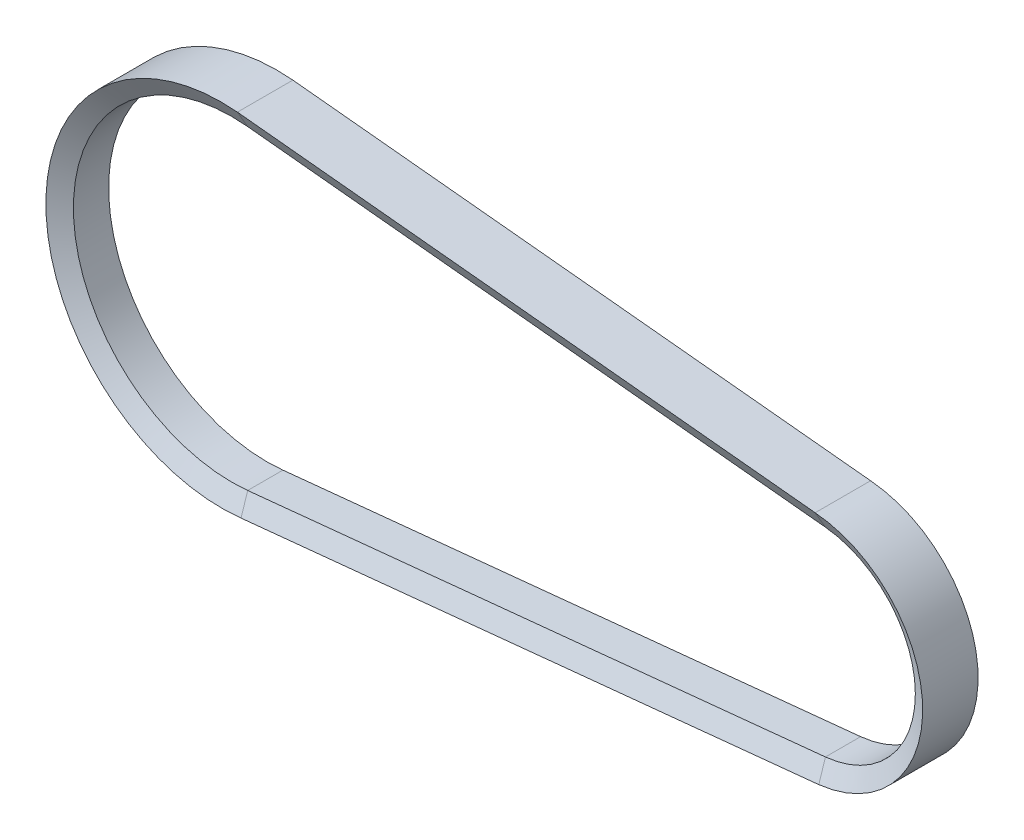
SolidWorks part; units mm, degrees
ref_plane "Front Plane" through (0, 0, 0) normal (0, 0, 1) x (1, 0, 0)
ref_plane "Top Plane" through (0, 0, 0) normal (0, 1, 0) x (1, 0, 0)
ref_plane "Right Plane" through (0, 0, 0) normal (1, 0, 0) x (0, 0, -1)
sketch "Sketch2" plane through (0, 0, 0) normal (0, 0, 1) x (1, 0, 0)
  line L0 (0, 0) -> (1, 0) construction
  line L1 (0, 0) -> (0, 1) construction
  line L2 (5.4, 53.7293) -> (203.4, 33.8296)
  line L3 (203.4, -33.8296) -> (5.4, -53.7293)
  arc A0 (5.4, -53.7293) -> (5.4, 53.7293) centre (0, 0) cw
  arc A1 (203.4, 33.8296) -> (203.4, -33.8296) centre (200, 0) cw
ref_plane "Plane1" through (5.4, 0, 0) normal (1, 0, 0) x (0, 0, -1)
sketch "Sketch3" plane through (5.4, 0, 0) normal (1, 0, 0) x (0, 0, -1)
  line L0 (-6.035, 54) -> (6.035, 54)
  line L1 (0, 54) -> (0, -54) construction
  line L2 (6.035, 54) -> (9.4991, 60)
  line L3 (9.4991, 60) -> (-9.4991, 60)
  line L4 (-9.4991, 60) -> (-6.035, 54)
  dimension "D1" = 12.07
  dimension "D2" = 6.035
  dimension "D3" = 54
  dimension "D4" = 6
  dimension "D5" = 60
  dimension "D6" = 60
sweep "Sweep1" add profiles "Sketch3" path "Sketch2"
